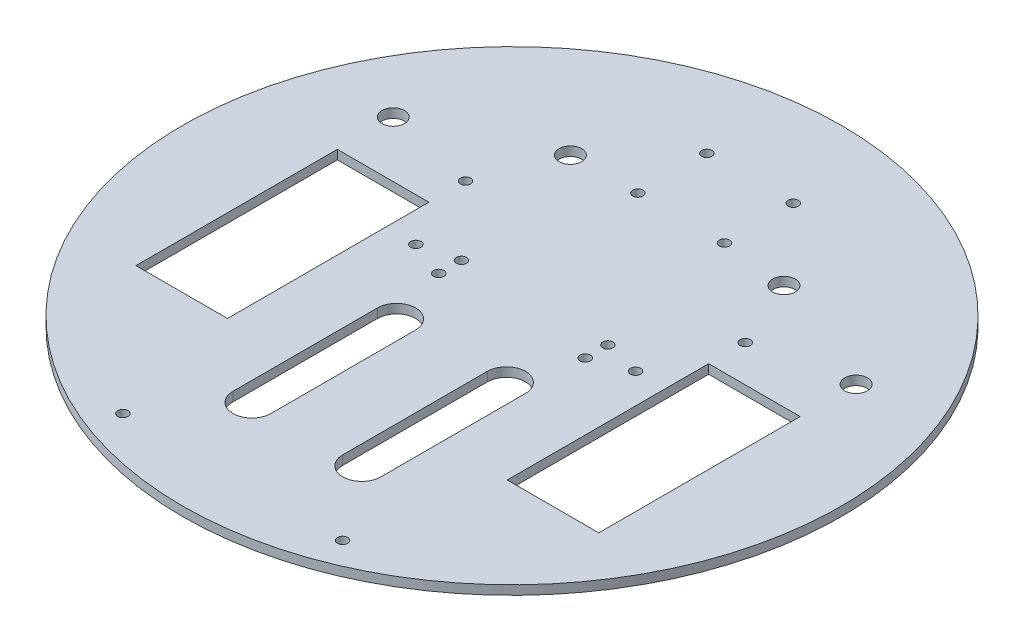
SolidWorks part; units mm, degrees
ref_plane "Front Plane" through (0, 0, 0) normal (0, 0, 1) x (1, 0, 0)
ref_plane "Top Plane" through (0, 0, 0) normal (0, 1, 0) x (1, 0, 0)
ref_plane "Right Plane" through (0, 0, 0) normal (1, 0, 0) x (0, 0, -1)
sketch "Sketch1" plane through (0, 0, 0) normal (0, 1, 0) x (1, 0, 0)
  line L0 (0, 114.3) -> (0, -114.3) construction
  line L1 (-114.3, 0) -> (114.3, 0) construction
  line L2 (-14.986, 82.55) -> (14.986, 82.55) construction
  line L3 (14.986, 82.55) -> (14.986, 58.674) construction
  line L4 (14.986, 58.674) -> (-14.986, 58.674) construction
  line L5 (-14.986, 58.674) -> (-14.986, 82.55) construction
  line L6 (25.4, 7.874) -> (-25.4, 7.874) construction
  line L7 (-25.4, 7.874) -> (-25.4, 0) construction
  line L8 (-25.4, 0) -> (25.4, 0) construction
  line L9 (25.4, 0) -> (25.4, 7.874) construction
  line L10 (25.4, 0) -> (114.3, 0) construction
  line L11 (48.514, 19.685) -> (80.264, 19.685)
  line L12 (48.514, 19.685) -> (48.514, -50.165)
  line L13 (48.514, -50.165) -> (80.264, -50.165)
  line L14 (80.264, 19.685) -> (80.264, -50.165)
  line L15 (48.514, 19.685) -> (80.264, -50.165) construction
  line L16 (48.514, -50.165) -> (80.264, 19.685) construction
  line L18 (-80.264, 19.685) -> (-48.514, 19.685)
  line L19 (-80.264, 19.685) -> (-80.264, -50.165)
  line L20 (-80.264, -50.165) -> (-48.514, -50.165)
  line L21 (-48.514, 19.685) -> (-48.514, -50.165)
  line L22 (-80.264, 19.685) -> (-48.514, -50.165) construction
  line L23 (-80.264, -50.165) -> (-48.514, 19.685) construction
  circle A0 centre (0, 0) radius 114.3
  circle A1 centre (-14.986, 82.55) radius 1.778
  circle A2 centre (14.986, 82.55) radius 1.778
  circle A3 centre (-14.986, 58.674) radius 1.778
  circle A4 centre (14.986, 58.674) radius 1.778
  circle A5 centre (25.4, 7.874) radius 1.778
  circle A6 centre (25.4, 0) radius 1.778
  circle A7 centre (-25.4, 7.874) radius 1.778
  circle A8 centre (-25.4, 0) radius 1.778
  point P15 (0, 82.55)
  point P24 (0, 7.874)
  point P26 (64.389, -15.24)
  point P33 (-64.389, -15.24)
  dimension "D1" = 228.6
  dimension "D2" = 3.556
  dimension "D5" = 7.874
  dimension "D3" = 29.972
  dimension "D4" = 23.876
  dimension "D6" = 23.114
  dimension "D7" = 31.75
  dimension "D8" = 69.85
  dimension "D9" = 15.24
  dimension "D10" = 31.75
  dimension "D11" = 50.8
  dimension "D12" = 50.8
extrude "Boss-Extrude1" add sketch "Sketch1" along normal blind 3.175
sketch "Sketch2" plane through (0, 3.175, 0) normal (0, 1, 0) x (1, 0, 0)
  line L0 (0, 4.7391) -> (0, -96.8609) construction
  line L1 (48.514, -50.165) -> (48.514, 32.385) construction
  line L2 (48.514, 32.385) -> (-48.514, 32.385) construction
  line L3 (-48.514, 32.385) -> (-48.514, -50.165) construction
  line L4 (-19.05, -71.1324) -> (-19.05, -20.9894) construction
  line L5 (38.1, 4.7391) -> (-38.1, 4.7391) construction
  line L6 (38.1, 4.7391) -> (38.1, -96.8609) construction
  line L7 (38.1, -96.8609) -> (-38.1, -96.8609) construction
  line L8 (-38.1, 4.7391) -> (-38.1, -96.8609) construction
  line L9 (-25.6746, -71.1324) -> (-25.6746, -20.9894)
  line L10 (-12.4254, -71.1324) -> (-12.4254, -20.9894)
  line L11 (19.05, -71.1324) -> (19.05, -20.9894) construction
  line L12 (12.4254, -71.1324) -> (12.4254, -20.9894)
  line L13 (25.6746, -71.1324) -> (25.6746, -20.9894)
  line L14 (-38.1, -46.0609) -> (0, -46.0609) construction
  line L15 (0, -46.0609) -> (38.1, -46.0609) construction
  line L16 (80.264, 19.685) -> (80.264, 39.0675) construction
  line L17 (80.264, 39.0675) -> (-80.264, 39.0675) construction
  line L18 (-80.264, 39.0675) -> (-80.264, 19.685) construction
  circle A0 centre (-48.514, 32.385) radius 1.778
  circle A1 centre (48.514, 32.385) radius 1.778
  circle A2 centre (14.986, 58.674) radius 1.778 construction
  circle A3 centre (38.1, 4.7391) radius 1.778
  circle A4 centre (-38.1, 4.7391) radius 1.778
  circle A5 centre (-38.1, -96.8609) radius 1.778
  circle A6 centre (38.1, -96.8609) radius 1.778
  arc A7 (-25.6746, -71.1324) -> (-12.4254, -71.1324) centre (-19.05, -71.1324) ccw
  arc A8 (-12.4254, -20.9894) -> (-25.6746, -20.9894) centre (-19.05, -20.9894) ccw
  arc A9 (12.4254, -71.1324) -> (25.6746, -71.1324) centre (19.05, -71.1324) ccw
  arc A10 (25.6746, -20.9894) -> (12.4254, -20.9894) centre (19.05, -20.9894) ccw
  circle A11 centre (-38.1, 58.3523) radius 3.9148
  circle A12 centre (38.1, 56.2303) radius 3.9148
  circle A13 centre (80.264, 39.0675) radius 3.9148
  circle A14 centre (-80.264, 39.0675) radius 3.9148
  point P24 (-19.05, -46.0609)
  point P35 (19.05, -46.0609)
  point P48 (-38.1, 58.3523)
  point P52 (0, 0)
  point P53 (38.1, 56.2303)
  dimension "D1" = 12.7
  dimension "D2" = 101.6
  dimension "D3" = 76.2
extrude "Cut-Extrude1" cut sketch "Sketch2" against normal blind 25.4
